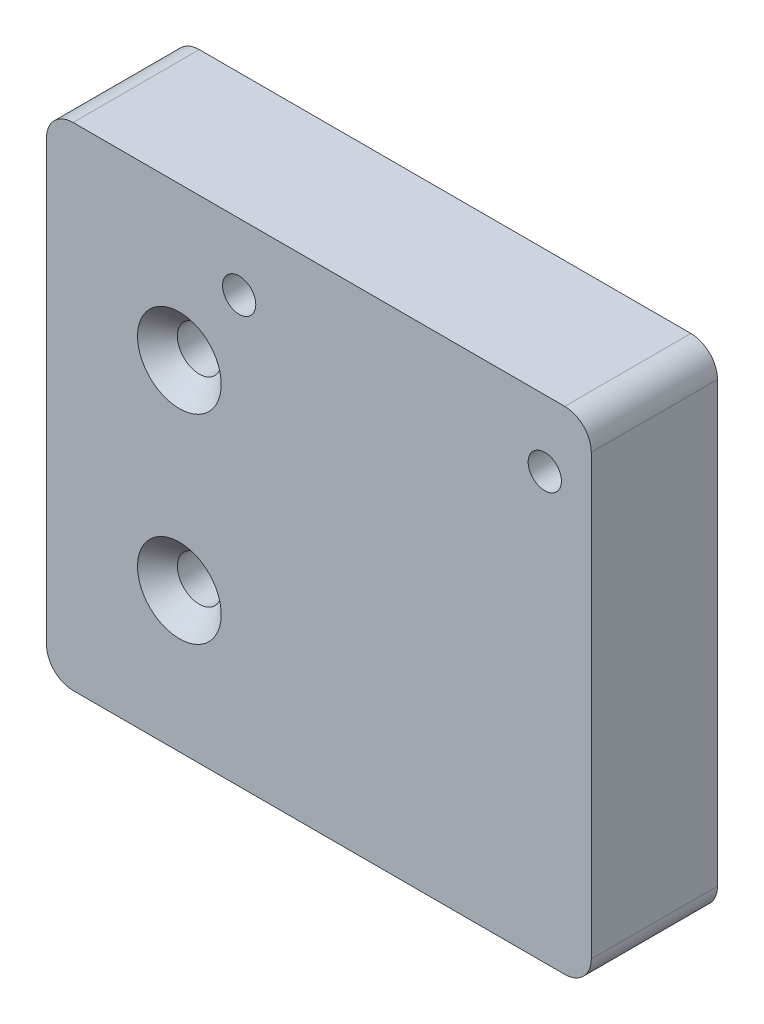
SolidWorks part; units mm, degrees
ref_plane "Front Plane" through (0, 0, 0) normal (0, 0, 1) x (1, 0, 0)
ref_plane "Top Plane" through (0, 0, 0) normal (0, 1, 0) x (1, 0, 0)
ref_plane "Right Plane" through (0, 0, 0) normal (1, 0, 0) x (0, 0, -1)
sketch "Sketch1" plane through (0, 0, 0) normal (0, 0, 1) x (1, 0, 0)
  line L1 (62, 72.839) -> (-20, 72.839)
  line L2 (62, 72.839) -> (62, 12.839)
  line L3 (62, 12.839) -> (-20, 12.839)
  line L4 (-20, 72.839) -> (-20, 12.839)
  dimension "D1" = 60
extrude "Boss-Extrude1" add sketch "Sketch1" along normal blind 19
hole_wizard "Tap Drill for M6 Tap1" positions "Sketch4" profile "Sketch3" hole size "M6" standard "ISO" end condition through all
sketch "Sketch4" plane through (0, 0, 19) normal (0, 0, 1) x (1, 0, 0)
  point P0 (9, 62.839)
  point P3 (55, 62.839)
sketch "Sketch3" plane through (9, 62.839, 19) normal (1, 0, 0) x (0, -1, 0)
  line L0 (0, 0) -> (0, 19)
  line L1 (0, 19) -> (2.5, 19)
  line L2 (2.5, 19) -> (2.5, 0)
  line L5 (2.5, 0) -> (0, 0)
  line L11 (0, -6.35) -> (0, 107.95) construction
  dimension "Thru Hole Dia." = 5
  dimension "Thru Hole Depth" = 19
hole_wizard "CSK for M6 Countersunk Flat Head Screw1" positions "Sketch5" profile "Sketch6" countersink size "M6" standard "ISO" end condition through all
sketch "Sketch5" plane through (0, 0, 19) normal (0, 0, 1) x (1, 0, 0)
  line L0 (-20, 12.839) -> (62, 12.839) construction
  point P0 (0, 19.839)
  point P2 (0, 49.839)
  dimension "D1" = 30
  dimension "D2" = 7
sketch "Sketch6" plane through (0, 19.839, 19) normal (1, 0, 0) x (0, -1, 0)
  line L0 (0, 0) -> (0, 19)
  line L1 (0, 19) -> (3.3, 19)
  line L2 (3.3, 19) -> (3.3, 3)
  line L3 (3.3, 3) -> (6.3, 0)
  line L5 (6.3, 0) -> (0, 0)
  line L6 (-3.3, 3) -> (-6.3, 0) construction
  line L11 (0, -6.35) -> (0, 107.95) construction
  dimension "Thru Hole Dia." = 6.6
  dimension "Thru Hole Depth" = 19
  dimension "Near C'Sink Dia." = 12.6
  dimension "Near C'Sink Angle" = 90
sketch "Sketch7" plane through (0, 0, 19) normal (0, 0, 1) x (1, 0, 0)
  line L0 (62, 12.839) -> (62, 72.839) construction
  line L1 (62, 12.8434) -> (-20, 12.8434)
  line L2 (62, 12.8434) -> (62, -1.211)
  line L3 (62, -1.211) -> (-20, -1.211)
  line L4 (-20, 12.8434) -> (-20, -1.211)
extrude "Boss-Extrude2" add sketch "Sketch7" against normal up to surface (19 mm away) up to face at (3.3, 19.839, 0)
hole_wizard "Tap Drill for M5 Tap1" positions "Sketch8" profile "Sketch9" hole size "M5" standard "ISO"
sketch "Sketch8" plane through (0, -1.211, 0) normal (0, -1, 0) x (-1, 0, 0)
  point P0 (-42, -9.5)
sketch "Sketch9" plane through (42, -1.211, 9.5) normal (1, 0, 0) x (0, 0, -1)
  line L0 (0, 0) -> (0, 31.2618)
  line L1 (0, 31.2618) -> (2.1, 30)
  line L2 (2.1, 30) -> (2.1, 0)
  line L5 (2.1, 0) -> (0, 0)
  line L10 (0, 31.2618) -> (-2.1, 30) construction
  line L11 (0, -6.35) -> (0, 107.95) construction
  dimension "Hole Dia." = 4.2
  dimension "Hole Depth" = 30
  dimension "Drill Angle" = 118
fillet "Fillet1" radius 4 4 edges at (-20, -1.211, 9.5) (62, 72.839, 9.5) (62, -1.211, 9.5) (-20, 72.839, 9.5)
